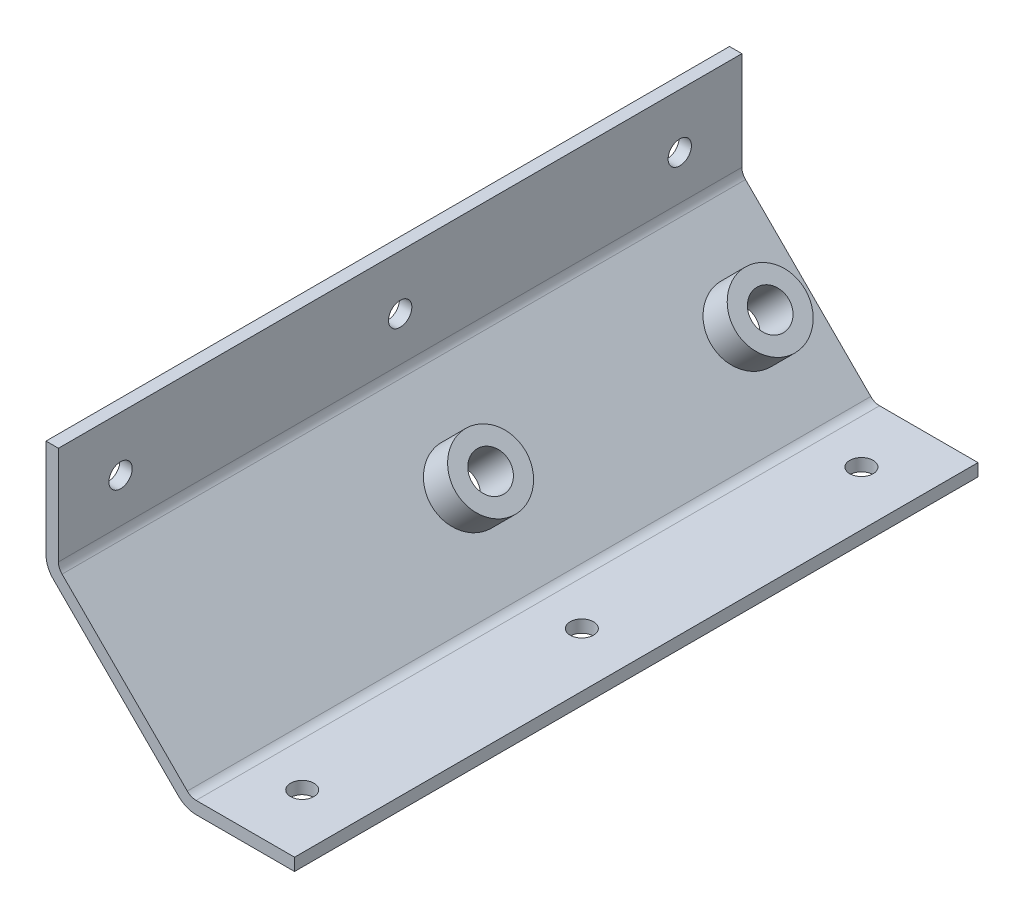
SolidWorks part; units mm, degrees
ref_plane "Front Plane" through (0, 0, 0) normal (0, 0, 1) x (1, 0, 0)
ref_plane "Top Plane" through (0, 0, 0) normal (0, 1, 0) x (1, 0, 0)
ref_plane "Right Plane" through (0, 0, 0) normal (1, 0, 0) x (0, 0, -1)
sketch "Sketch1" plane through (0, 0, 0) normal (0, 0, 1) x (1, 0, 0)
  line L0 (5980.8333, -6626.86) -> (6002.0062, -6626.86)
  line L1 (5979.7812, -6629.4) -> (6002.0062, -6629.4)
  line L2 (5953.7462, -6578.6) -> (5953.7462, -6599.7729)
  line L3 (5951.2062, -6578.6) -> (5951.2062, -6600.825)
  line L4 (5967.2898, -6613.3164) -> (5953.7462, -6599.7729)
  line L5 (5967.2898, -6613.3164) -> (5980.8333, -6626.86)
  line L6 (5965.4937, -6615.1125) -> (5967.2898, -6613.3164) construction
  line L7 (5979.7812, -6629.4) -> (5951.2062, -6600.825)
  line L8 (5951.2062, -6578.6) -> (5953.7462, -6578.6)
  line L9 (6002.0062, -6626.86) -> (6002.0062, -6629.4)
extrude "Extrude1" add sketch "Sketch1" along normal blind 139.7
sketch "Sketch2" plane through (0, -6629.4, 0) normal (0, -1, 0) x (1, 0, 0)
  line L0 (6002.0062, 69.85) -> (5990.881, 69.85) construction
  line L1 (6002.0062, 139.7) -> (6002.0062, 0) construction
  line L2 (5990.881, 69.85) -> (5990.881, 12.7) construction
  line L3 (5990.881, 69.85) -> (5990.881, 127) construction
  circle A0 centre (5990.881, 127) radius 2.3876
  circle A1 centre (5990.881, 69.85) radius 2.3876
  circle A2 centre (5990.881, 12.7) radius 2.3876
extrude "Cut-Extrude1" cut sketch "Sketch2" against normal up to surface (2.54 mm away) up to face at (5991.4198, -6626.86, 69.85)
sketch "Sketch3" plane through (5951.2062, 0, 0) normal (-1, 0, 0) x (0, 0, 1)
  line L0 (69.85, -6578.6) -> (69.85, -6589.7252) construction
  line L1 (139.7, -6578.6) -> (0, -6578.6) construction
  line L2 (69.85, -6589.7252) -> (127, -6589.7252) construction
  line L3 (69.85, -6589.7252) -> (12.7, -6589.7252) construction
  circle A0 centre (127, -6589.7252) radius 2.3876
  circle A1 centre (69.85, -6589.7252) radius 2.3876
  circle A2 centre (12.7, -6589.7252) radius 2.3876
extrude "Cut-Extrude2" cut sketch "Sketch3" against normal up to surface (2.54 mm away) up to face at (5953.7462, -6589.1864, 69.85)
sketch "Sketch4" plane through (-324.8094, -324.8094, 0) normal (-0.7071, -0.7071, 0) x (0, 0, 1)
  line L0 (69.85, -8875.6264) -> (69.85, -8916.0375) construction
  line L1 (139.7, -8875.6264) -> (0, -8875.6264) construction
  line L2 (139.7, -8916.0375) -> (0, -8916.0375) construction
  line L3 (69.85, -8895.832) -> (12.7, -8895.832) construction
  circle A0 centre (69.85, -8895.832) radius 3.81
  circle A1 centre (12.7, -8895.832) radius 3.81
extrude "Cut-Extrude3" cut sketch "Sketch4" against normal up to surface (2.54 mm away) up to face at (5967.2898, -6613.3164, 69.85)
sketch "Sketch5" plane through (-323.0133, -323.0133, 0) normal (0.7071, 0.7071, 0) x (0, 0, -1)
  circle A0 centre (-69.85, -8895.832) radius 3.81
  circle A1 centre (-69.85, -8895.832) radius 7.1755
  circle A2 centre (-12.7, -8895.832) radius 3.81
  circle A3 centre (-12.7, -8895.832) radius 7.1755
extrude "Extrude2" add sketch "Sketch5" along normal blind 6.985
fillet "Fillet1" radius 2.54 2 edges at (5953.7462, -6599.7729, 69.85) (5980.8333, -6626.86, 69.85)
fillet "Fillet2" radius 5.08 2 edges at (5979.7812, -6629.4, 69.85) (5951.2062, -6600.825, 69.85)
